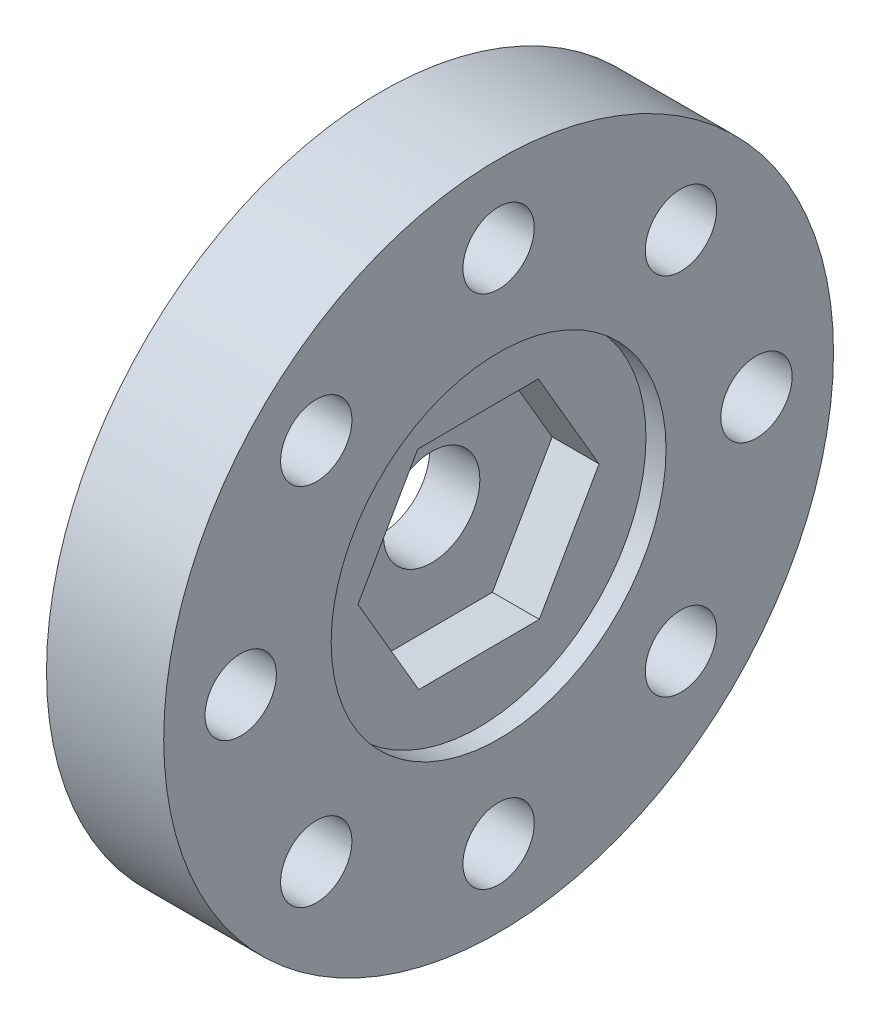
SolidWorks part; units mm, degrees
ref_plane "Front" through (0, 0, 0) normal (0, 0, 1) x (1, 0, 0)
ref_plane "Top" through (0, 0, 0) normal (0, 1, 0) x (1, 0, 0)
ref_plane "Right" through (0, 0, 0) normal (1, 0, 0) x (0, 0, -1)
sketch "Sketch1" plane through (0, 0, 0) normal (1, 0, 0) x (0, 0, -1)
  line L0 (0, 12.7) -> (0, 9.779) construction
  line L1 (0, 12.7) -> (0, 9.779) construction
  circle A0 centre (0, 0) radius 12.7
  circle A1 centre (0, 9.779) radius 1.3525
  circle A2 centre (6.9148, 6.9148) radius 1.3526
  circle A3 centre (9.779, 0) radius 1.3526
  circle A4 centre (6.9148, -6.9148) radius 1.3526
  circle A5 centre (0, -9.779) radius 1.3526
  circle A6 centre (-6.9148, -6.9148) radius 1.3526
  circle A7 centre (-9.779, 0) radius 1.3526
  circle A8 centre (-6.9148, 6.9148) radius 1.3526
  point P22 (0, 0)
  dimension "D1" = 25.4
  dimension "D3" = 2.7051
  dimension "D2" = 2.921
  dimension "D4" = 8
extrude "Boss-Extrude1" add sketch "Sketch1" along normal blind 4.445
sketch "Sketch2" plane through (4.445, 0, 0) normal (1, 0, 0) x (0, 0, -1)
  circle A0 centre (0, 0) radius 6.35
  dimension "D1" = 12.7
extrude "Cut-Extrude1" cut sketch "Sketch2" against normal blind 0.762
sketch "Sketch5" plane through (3.683, 0, 0) normal (1, 0, 0) x (0, 0, -1)
  line L0 (-0.0197, 3.9594) -> (-0.063, 12.6998) construction
  line L1 (-2.3056, 3.9481) -> (-4.5719, -0.0227)
  line L2 (-4.5719, -0.0227) -> (-2.2663, -3.9708)
  line L3 (-2.2663, -3.9708) -> (2.3056, -3.9481)
  line L4 (2.3056, -3.9481) -> (4.5719, 0.0227)
  line L5 (4.5719, 0.0227) -> (2.2663, 3.9708)
  line L6 (2.2663, 3.9708) -> (-2.3056, 3.9481)
  circle A0 centre (0, 0) radius 3.9595 construction
  circle A1 centre (0, 0) radius 12.7 construction
  dimension "D1" = 4.572
  dimension "D2" = 90
extrude "Cut-Extrude4" cut sketch "Sketch5" against normal blind 1.778
sketch "Sketch6" plane through (1.905, 0, 0) normal (1, 0, 0) x (0, 0, -1)
  circle A0 centre (0, 0) radius 1.8288
  dimension "D1" = 3.6576
extrude "Cut-Extrude5" cut sketch "Sketch6" against normal through all
